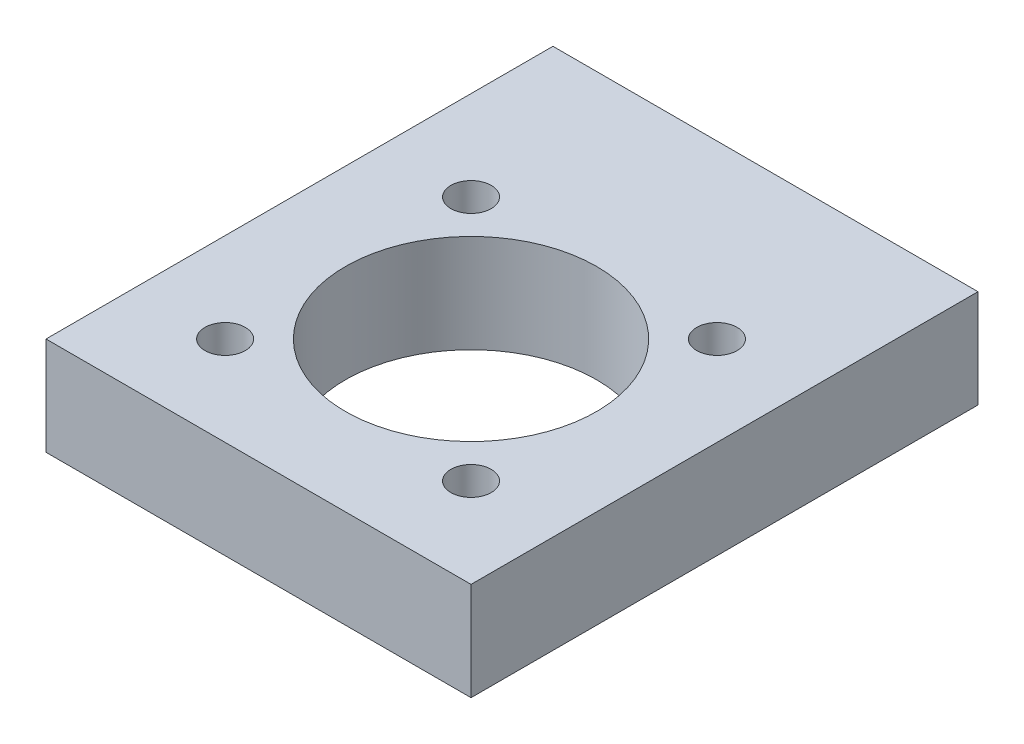
SolidWorks part; units mm, degrees
material "6061-T6 (SS)"
ref_plane "Front Plane" through (0, 0, 0) normal (0, 0, 1) x (1, 0, 0)
ref_plane "Top Plane" through (0, 0, 0) normal (0, 1, 0) x (1, 0, 0)
ref_plane "Right Plane" through (0, 0, 0) normal (1, 0, 0) x (0, 0, -1)
sketch "Sketch2" plane through (0, 0, 0) normal (0, 1, 0) x (1, 0, 0)
  line L0 (-27.5, 0) -> (-27.5, 38.1)
  line L1 (-27.5, 38.1) -> (27.5, 38.1)
  line L2 (27.5, 0) -> (27.5, 38.1)
  line L3 (-27.5, -27.5) -> (27.5, -27.5)
  line L4 (27.5, 0) -> (27.5, -27.5)
  line L5 (-27.5, -27.5) -> (-27.5, 0)
  arc A0 (-27.5, 0) -> (27.5, 0) centre (0, 0) ccw construction
  point P9 (0, -27.5)
  dimension "D1" = 55
  dimension "D2" = 38.1
extrude "Boss-Extrude1" add sketch "Sketch2" along normal blind 12.7
sketch "Sketch1" plane through (0, 0, 0) normal (0, 1, 0) x (1, 0, 0)
  line L0 (0, 0) -> (38.7669, 38.7669) construction
  line L1 (0, 0) -> (68.775, 0) construction
  line L2 (0, 0) -> (-35.9254, 35.9254) construction
  circle A0 centre (0, 0) radius 22.5 construction
  circle A1 centre (15.9099, 15.9099) radius 2.6099
  circle A5 centre (-15.9099, 15.9099) radius 2.6098
  circle A6 centre (15.9099, -15.9099) radius 2.6099
  circle A7 centre (-15.9099, -15.9099) radius 2.6098
  dimension "D1" = 45
  dimension "D2" = 5.2197
  dimension "D3" = 45
extrude "Cut-Extrude1" cut sketch "Sketch1" along normal up to next
sketch "Sketch3" plane through (0, 0, 0) normal (0, -1, 0) x (1, 0, 0)
  circle A0 centre (0, 0) radius 16.256
  dimension "D1" = 32.512
extrude "Cut-Extrude2" cut sketch "Sketch3" against normal up to next
sketch "Sketch4" plane through (0, 0, -38.1) normal (0, 0, -1) x (-1, 0, 0)
  line L1 (-40.2, 0) -> (40.2, 0)
  line L2 (-40.2, 0) -> (-40.2, 25.4)
  line L3 (-40.2, 25.4) -> (40.2, 25.4)
  line L4 (40.2, 0) -> (40.2, 25.4)
  point P4 (0, 0)
  dimension "D1" = 25.4
  dimension "D2" = 80.4
extrude "Boss-Extrude2" [suppressed] add sketch "Sketch4" against normal blind 6.35
sketch "Sketch5" plane through (0, 0, -38.1) normal (0, 0, -1) x (-1, 0, 0)
  line L0 (0, 0) -> (0, 25.2589) construction
  circle A2 centre (6.35, 6.35) radius 2.0193
  circle A3 centre (19.05, 6.35) radius 2.0193
  circle A4 centre (-19.05, 6.35) radius 2.0193
  circle A5 centre (-6.35, 6.35) radius 2.0193
  dimension "D3" = 4.0386
  dimension "D1" = 6.35
  dimension "D2" = 19.05
  dimension "D4" = 6.35
extrude "Cut-Extrude3" cut sketch "Sketch5" against normal blind 12.7
